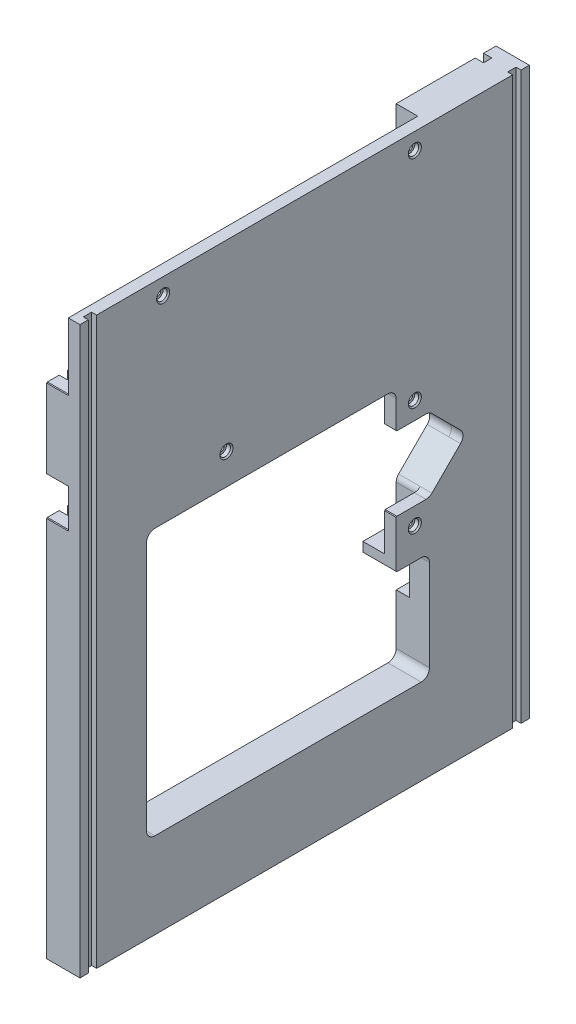
SolidWorks part; units mm, degrees
ref_plane "Front Plane" through (0, 0, 0) normal (0, 0, 1) x (1, 0, 0)
ref_plane "Top Plane" through (0, 0, 0) normal (0, 1, 0) x (1, 0, 0)
ref_plane "Right Plane" through (0, 0, 0) normal (1, 0, 0) x (0, 0, -1)
sketch "Sketch2" plane through (0, 0, 0) normal (1, 0, 0) x (0, 0, -1)
  line L1 (-215.489, 137.2751) -> (127.411, 137.2751)
  line L2 (-215.489, 137.2751) -> (-215.489, -294.5249)
  line L3 (-215.489, -294.5249) -> (127.411, -294.5249)
  line L4 (127.411, 137.2751) -> (127.411, -294.5249)
  dimension "D1" = 342.9
  dimension "D2" = 431.8
extrude "Base" add sketch "Sketch2" along normal blind 25.4
sketch "Sketch3" plane through (0, 0, 0) normal (1, 0, 0) x (0, 0, -1)
  line L0 (-44.039, -294.5249) -> (-44.039, 137.2751) construction
  line L1 (-215.489, -294.5249) -> (127.411, -294.5249) construction
  line L2 (-164.689, -25.9199) -> (-164.689, -229.1199)
  line L3 (-164.689, -229.1199) -> (51.211, -229.1199)
  line L4 (51.211, -146.9509) -> (51.211, -229.1199)
  line L5 (127.411, 137.2751) -> (-215.489, 137.2751) construction
  line L7 (-215.489, 137.2751) -> (-215.489, -294.5249) construction
  line L9 (51.211, -146.9509) -> (25.811, -146.9509)
  line L13 (-164.689, -25.9199) -> (25.811, -25.9199)
  line L14 (25.811, -146.9509) -> (25.811, -25.9199)
  dimension "D1" = 25.4
  dimension "D2" = 163.195
  dimension "D3" = 50.8
  dimension "D4" = 121.031
  dimension "D5" = 190.5
  dimension "D6" = 203.2
extrude "Cut-Extrude3" cut sketch "Sketch3" along normal up to next
sketch "Sketch4" plane through (0, 0, 0) normal (1, 0, 0) x (0, 0, -1)
  line L0 (-215.489, 137.2751) -> (-215.489, -294.5249) construction
  line L1 (19.461, -18.2999) -> (-158.339, -18.2999)
  line L2 (51.211, -15.1249) -> (51.211, 137.2751)
  line L3 (51.211, 137.2751) -> (-202.789, 137.2751)
  line L4 (-164.689, -12.5837) -> (-164.689, -3.0599)
  line L5 (51.211, -146.9509) -> (25.811, -146.9509) construction
  line L6 (25.811, -25.9199) -> (-164.689, -25.9199) construction
  line L7 (-164.689, 25.5151) -> (-215.489, 25.5151)
  line L8 (51.211, -15.1249) -> (51.211, -53.8599)
  line L9 (44.861, -139.3309) -> (25.811, -139.3309)
  line L10 (25.811, -25.9199) -> (25.811, -139.3309)
  line L11 (25.811, -25.9199) -> (-164.689, -25.9199) construction
  line L12 (25.811, -25.9199) -> (19.461, -25.9199)
  line L13 (19.461, -18.2999) -> (19.461, -25.9199)
  line L14 (51.211, -136.1559) -> (51.211, -146.9509)
  line L15 (51.211, -146.9509) -> (44.861, -146.9509)
  line L16 (44.861, -139.3309) -> (44.861, -146.9509)
  line L17 (-44.039, 137.2751) -> (-44.039, -294.5249) construction
  line L18 (-164.689, -12.5837) -> (-164.689, -25.9199)
  line L19 (-164.689, -25.9199) -> (-158.339, -25.9199)
  line L20 (-158.339, -18.2999) -> (-158.339, -25.9199)
  line L22 (-215.489, -294.5249) -> (127.411, -294.5249) construction
  line L23 (51.211, -110.2479) -> (79.405, -82.0539)
  line L24 (-164.689, -3.0599) -> (-215.489, -3.0599)
  line L25 (-215.489, 25.5151) -> (-215.489, -3.0599)
  line L26 (-164.689, 25.5151) -> (-164.689, 86.4751)
  line L27 (-202.789, 137.2751) -> (-215.489, 137.2751)
  line L28 (79.405, -82.0539) -> (51.211, -53.8599)
  line L29 (-164.689, 86.4751) -> (-215.489, 86.4751)
  line L30 (-215.489, 137.2751) -> (-215.489, 90.2851)
  line L31 (-215.489, 90.2851) -> (-215.489, 86.4751)
  line L32 (51.211, -110.2479) -> (51.211, -136.1559)
  dimension "D2" = 7.62
  dimension "D3" = 15.24
  dimension "D4" = 276.606
  dimension "D5" = 25.4
  dimension "D6" = 6.35
  dimension "D7" = 6.35
  dimension "D8" = 7.62
  dimension "D9" = 6.35
  dimension "D10" = 50.8
  dimension "D11" = 111.76
  dimension "D12" = 215.9
  dimension "D13" = 266.7
  dimension "D15" = 45
  dimension "D16" = 29.083
  dimension "D17" = 56.388
extrude "NC pocket" cut sketch "Sketch4" along normal blind 16.51
fillet "Fillet9" radius 6.35 2 edges at (8.255, -110.2479, -51.211) (8.255, -53.8599, -51.211)
fillet "Fillet6" radius 6.35 1 edges at (8.255, -82.0539, -79.405)
hole_wizard "CBORE for M4 SHCS1" positions "Sketch8" profile "Sketch10" counterbore size "M4" standard "ANSI Metric" end condition up to next
sketch "Sketch8" plane through (25.4, 0, 0) normal (1, 0, 0) x (0, 0, -1)
  line L1 (127.411, 137.2751) -> (-215.489, 137.2751) construction
  line L4 (-164.689, -3.0599) -> (-164.689, -229.1199) construction
  line L5 (51.211, -229.1199) -> (51.211, -112.8782) construction
  line L6 (-158.339, -18.2999) -> (19.461, -18.2999) construction
  point P0 (-151.989, 124.5751)
  point P5 (40.035, 124.5751)
  point P7 (40.035, -123.4559)
  point P9 (40.035, -40.5249)
  point P11 (-103.729, -2.4249)
  dimension "D2" = 12.7
  dimension "D3" = 12.7
  dimension "D4" = 11.176
  dimension "D5" = 60.96
  dimension "D6" = 15.875
  dimension "D7" = 11.176
  dimension "D8" = 165.1
  dimension "D9" = 11.176
  dimension "D10" = 82.931
  dimension "D11" = 12.7
sketch "Sketch10" plane through (25.4, 124.5751, 151.989) normal (0, 1, 0) x (0, 0, -1)
  line L0 (0, 0) -> (0, 8.89)
  line L1 (0, 8.89) -> (2.15, 8.89)
  line L3 (2.15, 8.89) -> (2.15, 4)
  line L4 (4, 4) -> (2.15, 4)
  line L5 (4, 4) -> (4, 1)
  line L6 (4, 1) -> (5, 0)
  line L7 (5, 0) -> (0, 0)
  line L8 (-4, 1) -> (-5, 0) construction
  line L11 (0, -6.35) -> (0, 107.95) construction
  dimension "Thru Hole Dia." = 4.3
  dimension "Thru Hole Depth" = 8.89
  dimension "C'Bore Dia." = 8
  dimension "C'Bore Depth" = 4
  dimension "Near C'Sink Dia." = 10
  dimension "Near C'Sink Angle" = 90
sketch "Sketch18" plane through (16.51, 0, 0) normal (-1, 0, 0) x (0, 0, 1)
  circle A0 centre (-40.035, 124.5751) radius 7.1755
  circle A1 centre (151.989, 124.5751) radius 7.1755
  circle A2 centre (103.729, -2.4249) radius 7.1755
  circle A3 centre (-40.035, -40.5249) radius 7.1755
  circle A4 centre (-40.035, -123.4559) radius 7.1755
  dimension "D1" = 14.351
  dimension "D2" = 14.351
  dimension "D3" = 14.351
  dimension "D4" = 14.351
  dimension "D5" = 14.351
extrude "Cut-Extrude4" cut sketch "Sketch18" against normal blind 1.016
hole_wizard "3/8-16 Tapped Hole1" positions "3DSketch1" profile "Sketch14" tap size "3/8-16" standard "ANSI Inch"
sketch3d "3DSketch1"
  line L0 (0, -294.5249, 215.489) -> (0, -294.5249, -127.411) construction
  line L1 (25.4, -294.5249, 215.489) -> (0, -294.5249, 215.489) construction
  point P0 (12.7, -294.5249, -70.261)
  point P2 (12.7, -294.5249, 44.039)
  point P4 (12.7, -294.5249, 158.339)
  dimension "D1" = 12.7
  dimension "D2" = 12.7
  dimension "D3" = 12.7
  dimension "D4" = 114.3
  dimension "D6" = 114.3
  dimension "D5" = 171.45
sketch "Sketch14" plane through (12.7, -294.5249, -70.261) normal (1, 0, 0) x (0, 0, -1)
  line L0 (0, 0) -> (0, 30.3247)
  line L1 (0, 30.3247) -> (3.9687, 27.94)
  line L2 (3.9687, 27.94) -> (3.9687, 0)
  line L5 (3.9687, 0) -> (0, 0)
  line L10 (0, 30.3247) -> (-3.9688, 27.94) construction
  line L11 (0, -6.35) -> (0, 107.95) construction
  dimension "Tap Drill Dia." = 7.9375
  dimension "Tap Drill Depth" = 27.94
  dimension "Drill Angle" = 118
cosmetic thread "Hole Thread1" parameters "D1"=25.4, "D2"=9.525
cosmetic thread "Hole Thread2" parameters "D1"=25.4, "D2"=9.525
cosmetic thread "Hole Thread3" parameters "D1"=25.4, "D2"=9.525
hole_wizard "3/8-16 Tapped Hole2" positions "Sketch15" profile "Sketch17" tap size "3/8-16" standard "ANSI Inch"
sketch "Sketch15" plane through (0, 0, 0) normal (-1, 0, 0) x (0, 0, 1)
  line L0 (215.489, -3.0599) -> (215.489, -294.5249) construction
  line L1 (-127.411, -294.5249) -> (-127.411, 137.2751) construction
  line L2 (215.489, -294.5249) -> (-127.411, -294.5249) construction
  point P0 (188.5015, -220.8649)
  point P2 (188.5015, -162.4449)
  point P4 (-100.4235, -220.8649)
  point P6 (-100.4235, -162.4449)
  dimension "D1" = 26.9875
  dimension "D2" = 26.9875
  dimension "D3" = 26.9875
  dimension "D4" = 26.9875
  dimension "D5" = 73.66
  dimension "D6" = 58.42
  dimension "D7" = 58.42
  dimension "D8" = 73.66
cosmetic thread "Hole Thread4" parameters "D1"=17.78, "D2"=9.525
cosmetic thread "Hole Thread5" parameters "D1"=17.78, "D2"=9.525
cosmetic thread "Hole Thread6" parameters "D1"=17.78, "D2"=9.525
cosmetic thread "Hole Thread7" parameters "D1"=17.78, "D2"=9.525
sketch "Sketch17" plane through (0, -220.8649, 188.5015) normal (0, 1, 0) x (0, 0, 1)
  line L0 (0, 0) -> (0, 22.7047)
  line L1 (0, 22.7047) -> (3.9687, 20.32)
  line L2 (3.9687, 20.32) -> (3.9687, 0)
  line L5 (3.9687, 0) -> (0, 0)
  line L10 (0, 22.7047) -> (-3.9688, 20.32) construction
  line L11 (0, -6.35) -> (0, 107.95) construction
  dimension "Tap Drill Dia." = 7.9375
  dimension "Tap Drill Depth" = 20.32
  dimension "Drill Angle" = 118
sketch "Sketch20" plane through (16.51, 0, 0) normal (-1, 0, 0) x (0, 0, 1)
  line L0 (-51.211, -53.8599) -> (-25.811, -53.8599)
  line L2 (-51.211, -53.8599) -> (-79.405, -82.0539)
  line L3 (-79.405, -82.0539) -> (-51.211, -110.2479)
  line L4 (-25.811, -25.9199) -> (-25.811, -139.3309) construction
  line L6 (-25.811, -53.8599) -> (-25.811, -110.2479)
  line L7 (-25.811, -110.2479) -> (-51.211, -110.2479)
  line L8 (-51.211, -45.3946) -> (-51.211, -54.9122) construction
  line L9 (-51.211, -51.2297) -> (-51.211, 137.2751) construction
  line L10 (-51.211, -116.8371) -> (-51.211, -107.9924) construction
  line L11 (-51.211, -146.9509) -> (-51.211, -112.8782) construction
  line L12 (-74.9149, -77.5638) -> (-53.0709, -55.7198) construction
  line L13 (-53.0709, -108.388) -> (-74.9149, -86.544) construction
extrude "Cut-Extrude5" cut sketch "Sketch20" against normal up to next
fillet "Fillet1" radius 6.35 5 edges at (20.955, -25.9199, 164.689) (12.7, -229.1199, 164.689) (12.7, -229.1199, -51.211) (20.955, -146.9509, -51.211) (20.955, -25.9199, -25.811)
fillet "Fillet2" radius 6.35 3 edges at (20.955, -82.0539, -79.405) (20.955, -110.2479, -51.211) (20.955, -53.8599, -51.211)
chamfer "Chamfer1" distance 0.508 angle 45 9 edges at (8.255, -3.0599, 215.489) (8.255, -3.0599, 164.689) (8.255, 25.5151, 215.489) (8.255, 25.5151, 164.689) (8.255, 86.4751, 215.489) (8.255, 86.4751, 164.689) (12.7, -146.9509, -25.811) (20.955, -110.2479, -25.811) (20.955, -53.8599, -25.811)
sketch "Sketch21" plane through (0, 0, 0) normal (-1, 0, 0) x (0, 0, 1)
  line L0 (215.489, -294.5249) -> (-127.411, -294.5249) construction
  line L1 (205.964, -294.5249) -> (199.614, -294.5249)
  line L2 (205.964, -294.5249) -> (205.964, 137.2751)
  line L3 (205.964, 137.2751) -> (199.614, 137.2751)
  line L4 (199.614, -294.5249) -> (199.614, 137.2751)
  line L5 (-127.411, 137.2751) -> (-51.211, 137.2751) construction
  line L6 (215.489, -3.5679) -> (215.489, -294.5249) construction
  line L7 (-127.411, -294.5249) -> (-127.411, 137.2751) construction
  line L8 (-111.536, -294.5249) -> (-117.886, -294.5249)
  line L9 (-111.536, -294.5249) -> (-111.536, 137.2751)
  line L10 (-111.536, 137.2751) -> (-117.886, 137.2751)
  line L11 (-117.886, -294.5249) -> (-117.886, 137.2751)
  dimension "D1" = 6.35
  dimension "D2" = 9.525
  dimension "D3" = 6.35
  dimension "D4" = 9.525
extrude "Cut-Extrude6" cut sketch "Sketch21" against normal blind 6.35
sketch "Sketch22" plane through (25.4, 0, 0) normal (1, 0, 0) x (0, 0, -1)
  line L0 (-215.489, -294.5249) -> (127.411, -294.5249) construction
  line L1 (-202.789, -294.5249) -> (-209.139, -294.5249)
  line L2 (-202.789, -294.5249) -> (-202.789, 137.2751)
  line L3 (-202.789, 137.2751) -> (-209.139, 137.2751)
  line L4 (-209.139, -294.5249) -> (-209.139, 137.2751)
  line L5 (127.411, 137.2751) -> (-215.489, 137.2751) construction
  line L6 (-215.489, 137.2751) -> (-215.489, -294.5249) construction
  line L7 (127.411, -294.5249) -> (127.411, 137.2751) construction
  line L8 (114.711, 137.2751) -> (121.061, 137.2751)
  line L9 (114.711, 137.2751) -> (114.711, -294.5249)
  line L10 (114.711, -294.5249) -> (121.061, -294.5249)
  line L11 (121.061, 137.2751) -> (121.061, -294.5249)
  dimension "D1" = 6.35
  dimension "D2" = 6.35
  dimension "D3" = 6.35
  dimension "D4" = 6.35
extrude "Cut-Extrude7" cut sketch "Sketch22" against normal blind 3.81
sketch "Sketch23" plane through (0, 0, 0) normal (-1, 0, 0) x (0, 0, 1)
  line L0 (-51.211, -222.7699) -> (-51.211, -112.8782) construction
  line L1 (-51.211, -135.7749) -> (-84.231, -135.7749)
  line L2 (-51.211, -135.7749) -> (-51.211, -184.0349)
  line L3 (-51.211, -184.0349) -> (-84.231, -184.0349)
  line L4 (-84.231, -135.7749) -> (-84.231, -184.0349)
  line L5 (-111.536, 137.2751) -> (-51.211, 137.2751) construction
  dimension "D1" = 33.02
  dimension "D2" = 48.26
  dimension "D3" = 273.05
extrude "Cut-Extrude8" cut sketch "Sketch23" against normal blind 10.16
fillet "Fillet10" radius 6.35 2 edges at (5.08, -135.7749, -84.231) (5.08, -184.0349, -84.231)
